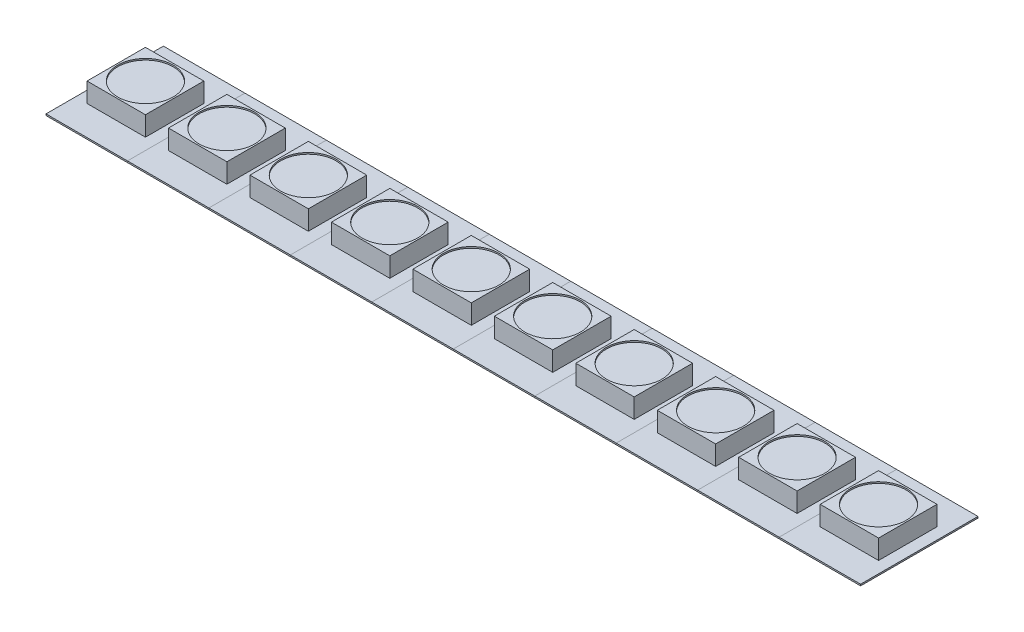
SolidWorks part; units mm, degrees
ref_plane "Front Plane" through (0, 0, 0) normal (0, 0, 1) x (1, 0, 0)
ref_plane "Top Plane" through (0, 0, 0) normal (0, 1, 0) x (1, 0, 0)
ref_plane "Right Plane" through (0, 0, 0) normal (1, 0, 0) x (0, 0, -1)
sketch "Sketch1" plane through (0, 0, 0) normal (0, 1, 0) x (1, 0, 0)
  line L0 (-3.4544, 4.9784) -> (3.4544, -4.9784) construction
  line L1 (-3.4544, 4.9784) -> (3.4544, 4.9784)
  line L2 (-3.4544, 4.9784) -> (-3.4544, -4.9784)
  line L3 (-3.4544, -4.9784) -> (3.4544, -4.9784)
  line L4 (3.4544, 4.9784) -> (3.4544, -4.9784)
  dimension "D1" = 9.9568
  dimension "D2" = 6.9088
extrude "Boss-Extrude1" add sketch "Sketch1" along normal blind 0.127
sketch "Sketch3" plane through (0, 0.127, 0) normal (0, 1, 0) x (1, 0, 0)
  line L0 (-3.4544, 4.9784) -> (3.4544, -4.9784) construction
  line L1 (-2.4765, 2.4765) -> (2.4765, -2.4765) construction
  line L2 (-2.4765, 2.4765) -> (2.4765, 2.4765)
  line L3 (-2.4765, 2.4765) -> (-2.4765, -2.4765)
  line L4 (-2.4765, -2.4765) -> (2.4765, -2.4765)
  line L5 (2.4765, 2.4765) -> (2.4765, -2.4765)
  dimension "D1" = 4.953
extrude "Boss-Extrude3" add sketch "Sketch3" along normal blind 1.651
sketch "Sketch5" plane through (0, 1.778, 0) normal (0, 1, 0) x (1, 0, 0)
  circle A0 centre (0, 0) radius 2.3483
extrude "Cut-Extrude1" cut sketch "Sketch5" against normal blind 0.127
pattern_linear "LPattern1" count 10 spacing 6.9088 along (1, 0, 0) of "Boss-Extrude3", "Cut-Extrude1", "Boss-Extrude1"
